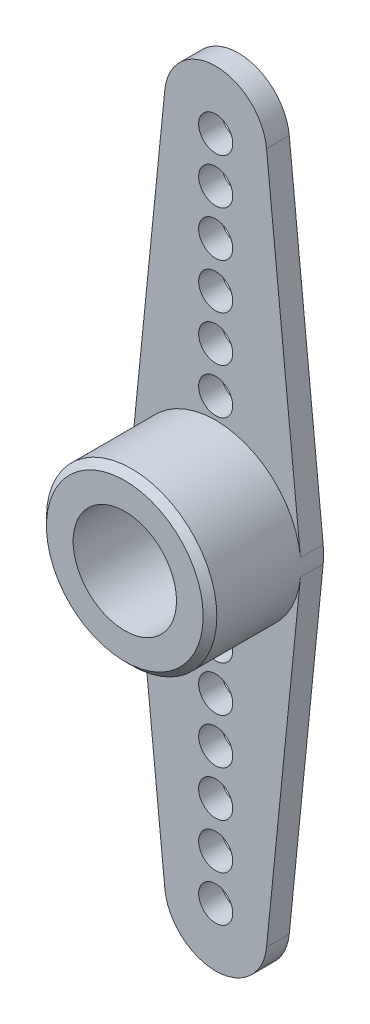
SolidWorks part; units mm, degrees
ref_plane "Plan de face" through (0, 0, 0) normal (0, 0, 1) x (1, 0, 0)
ref_plane "Plan de dessus" through (0, 0, 0) normal (0, 1, 0) x (1, 0, 0)
ref_plane "Plan de droite" through (0, 0, 0) normal (1, 0, 0) x (0, 0, -1)
sketch "Esquisse1" plane through (0, 0, 0) normal (0, 0, 1) x (1, 0, 0)
  line L0 (-25.8199, 1.564) -> (18.3852, 1.564) construction
  line L1 (0, 0) -> (0, 15) construction
  line L2 (-2.2387, 15.225) -> (-3.7312, 0.375)
  line L3 (2.2387, 15.225) -> (3.7312, 0.375)
  arc A0 (-3.7312, 0.375) -> (3.7312, 0.375) centre (0, 0) ccw
  arc A1 (2.2387, 15.225) -> (-2.2387, 15.225) centre (0, 15) ccw
  dimension "D1" = 7.5
  dimension "D3" = 4.5
  dimension "D2" = 15
extrude "Boss.-Extru.1" add sketch "Esquisse1" along normal blind 1
sketch "Esquisse2" plane through (0, 0, 1) normal (0, 0, 1) x (1, 0, 0)
  circle A0 centre (0, 0) radius 3.75
extrude "Boss.-Extru.2" add sketch "Esquisse2" along normal blind 4
sketch "Esquisse3" plane through (0, 0, 5) normal (0, 0, 1) x (1, 0, 0)
  circle A0 centre (0, 0) radius 2.275
  dimension "D1" = 4.55
extrude "Enlèv. mat.-Extru.1" cut sketch "Esquisse3" against normal blind 3.5
sketch "Esquisse4" plane through (0, 0, 0) normal (0, 0, -1) x (-1, 0, 0)
  circle A0 centre (0, 0) radius 2
  dimension "D1" = 4
extrude "Enlèv. mat.-Extru.2" cut sketch "Esquisse4" against normal blind 0.8
sketch "Esquisse5" plane through (0, 0, 0.8) normal (0, 0, -1) x (-1, 0, 0)
  circle A0 centre (0, 0) radius 0.75
  dimension "D1" = 1.5
extrude "Enlèv. mat.-Extru.3" cut sketch "Esquisse5" against normal blind 4.8
sketch "Esquisse6" plane through (0, 0, 0) normal (0, 0, -1) x (-1, 0, 0)
  circle A0 centre (0, 4.6722) radius 0.75
  circle A1 centre (0, 6.6722) radius 0.75
  circle A2 centre (0, 8.6722) radius 0.75
  circle A3 centre (0, 10.6722) radius 0.75
  circle A4 centre (0, 12.6722) radius 0.75
  circle A5 centre (0, 14.6722) radius 0.75
  dimension "D1" = 1.5
  dimension "D2" = 6
extrude "Enlèv. mat.-Extru.4" cut sketch "Esquisse6" against normal blind 4.8
chamfer "Chanfrein1" distance 0.3 angle 45 1 edges at (3.75, 0, 5)
sketch "Esquisse7" plane through (0, 0, 0) normal (0, 0, -1) x (-1, 0, 0)
  line L1 (-5.1566, 0) -> (4.1871, 0)
  line L2 (-5.1566, 0) -> (-5.1566, -4.6714)
  line L3 (-5.1566, -4.6714) -> (4.1871, -4.6714)
  line L4 (4.1871, 0) -> (4.1871, -4.6714)
extrude "Enlèv. mat.-Extru.5" cut sketch "Esquisse7" against normal blind 10
mirror "Symétrie1" about plane through (5.1566, 0, 10) normal (0, 1, 0) of bodies 107
